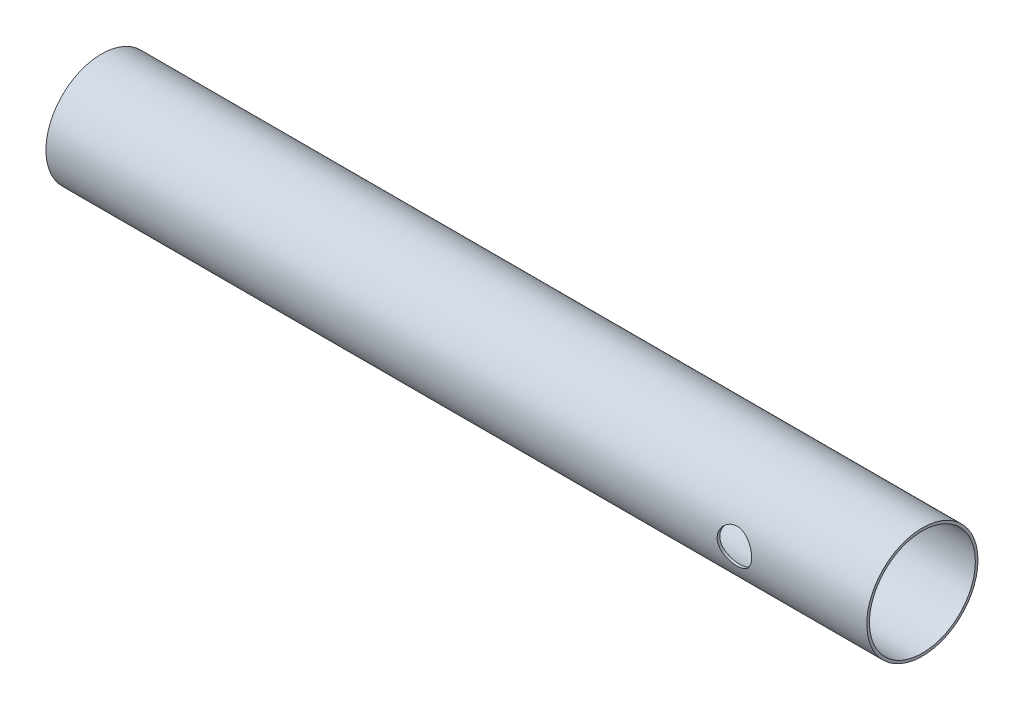
SolidWorks part; units mm, degrees
material "Aleación 1060"
ref_plane "Alzado" through (0, 0, 0) normal (0, 0, 1) x (1, 0, 0)
ref_plane "Planta" through (0, 0, 0) normal (0, 1, 0) x (1, 0, 0)
ref_plane "Vista lateral" through (0, 0, 0) normal (1, 0, 0) x (0, 0, -1)
sketch "Croquis1" plane through (0, 0, 0) normal (1, 0, 0) x (0, 0, -1)
  circle A0 centre (0, 0) radius 10.5
  dimension "D1" = 21
extrude "Saliente-Extruir1" add sketch "Croquis1" along normal blind 155
sketch "Croquis2" plane through (155, 0, 0) normal (1, 0, 0) x (0, 0, -1)
  circle A0 centre (0, 0) radius 10
  dimension "D1" = 20
extrude "Cortar-Extruir1" cut sketch "Croquis2" against normal blind 155
sketch3d "Croquis3D1"
  point P0 (135.5673, -1.6473, 10.37)
ref_plane "Plano1" through (0, 0, 10.37) normal (0, 0, 1) x (1, 0, 0)
sketch "Croquis3" plane through (0, 0, 10.37) normal (0, 0, 1) x (1, 0, 0)
  line L0 (155, -10.5) -> (155, 10.5) construction
  circle A0 centre (130, 0) radius 3.25
  dimension "D1" = 6.5
  dimension "D2" = 25
extrude "Cortar-Extruir2" cut sketch "Croquis3" against normal mid plane 5
